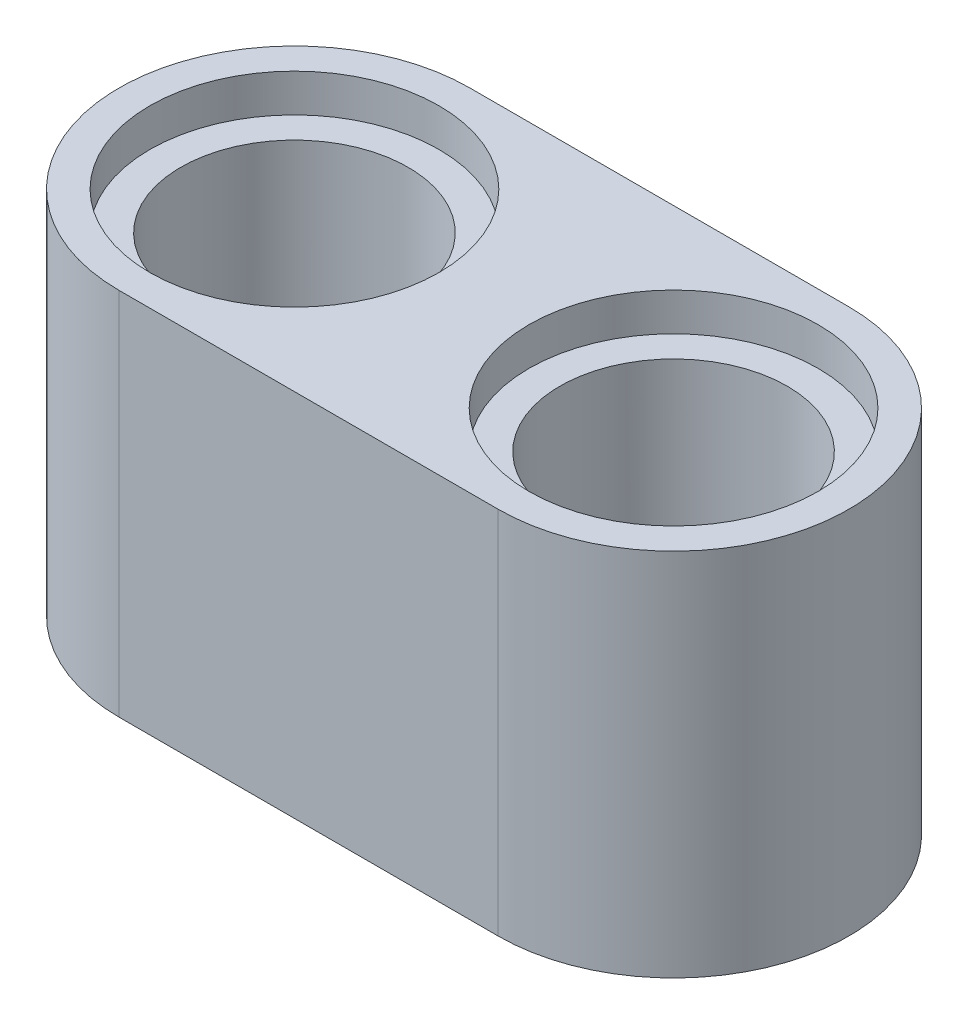
SolidWorks part; units mm, degrees
ref_plane "Front Plane" through (0, 0, 0) normal (0, 0, 1) x (1, 0, 0)
ref_plane "Top Plane" through (0, 0, 0) normal (0, 1, 0) x (1, 0, 0)
ref_plane "Right Plane" through (0, 0, 0) normal (1, 0, 0) x (0, 0, -1)
sketch "Sketch1" plane through (0, 0, 0) normal (0, 1, 0) x (1, 0, 0)
  line L1 (-16, 3.7) -> (-8, 3.7)
  line L4 (-8, -3.7) -> (-16, -3.7)
  arc A10 (-16, 3.7) -> (-16, -3.7) centre (-16, 0) ccw
  arc A11 (-8, 3.7) -> (-8, -3.7) centre (-8, 0) cw
  point P20 (8, -3.7)
  point P25 (-8, -3.7)
  dimension "D1" = 3.7
extrude "Boss-Extrude3" add sketch "Sketch1" along normal blind 7.8 contours L4 A10 L1 A11
sketch "Sketch2" plane through (0, 7.8, 0) normal (0, 1, 0) x (1, 0, 0)
  circle A6 centre (-16, 0) radius 2.4
  circle A9 centre (-8, 0) radius 2.4
  dimension "D1" = 4.8
  dimension "D2" = 8
extrude "Cut-Extrude6" cut sketch "Sketch2" against normal blind 7.8
sketch "Sketch3" plane through (0, 7.8, 0) normal (0, 1, 0) x (1, 0, 0)
  circle A3 centre (-16, 0) radius 3.05
  circle A4 centre (-8, 0) radius 3.05
  dimension "D1" = 6.1
  dimension "D2" = 8
extrude "Cut-Extrude7" cut sketch "Sketch3" against normal blind 0.8
sketch "Sketch4" plane through (0, 0, 0) normal (0, -1, 0) x (1, 0, 0)
  circle A3 centre (-16, 0) radius 3.05
  circle A4 centre (-8, 0) radius 3.05
  dimension "D1" = 6.1
  dimension "D2" = 8
extrude "Cut-Extrude8" cut sketch "Sketch4" against normal blind 0.8
